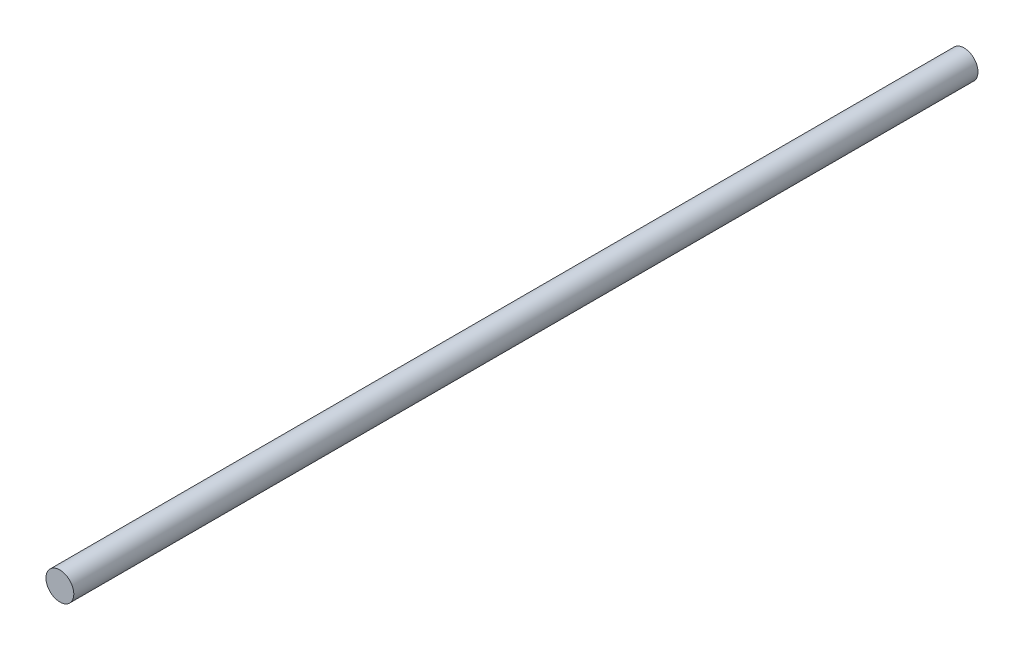
SolidWorks part; units mm, degrees
ref_plane "Front Plane" through (0, 0, 0) normal (0, 0, 1) x (1, 0, 0)
ref_plane "Top Plane" through (0, 0, 0) normal (0, 1, 0) x (1, 0, 0)
ref_plane "Right Plane" through (0, 0, 0) normal (1, 0, 0) x (0, 0, -1)
sketch "Sketch1" plane through (0, 0, 0) normal (0, 0, 1) x (1, 0, 0)
  circle A0 centre (0, 0) radius 2
extrude "Boss-Extrude1" add sketch "Sketch1" along normal blind 130
